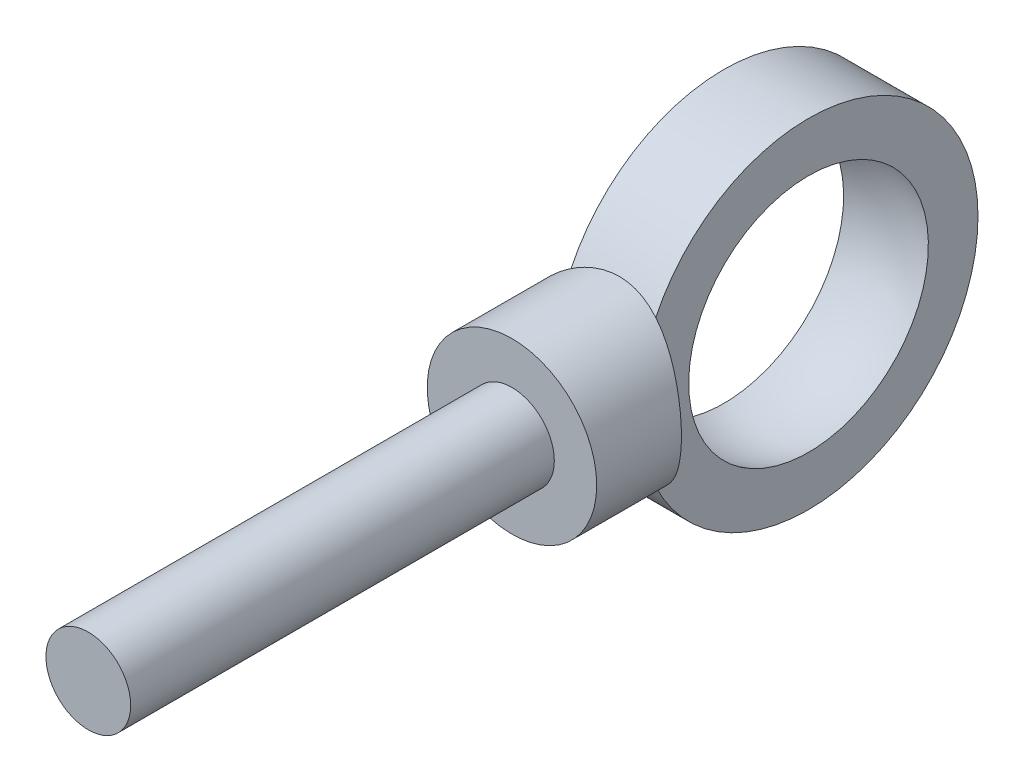
SolidWorks part; units mm, degrees
ref_plane "Front Plane" through (0, 0, 0) normal (0, 0, 1) x (1, 0, 0)
ref_plane "Top Plane" through (0, 0, 0) normal (0, 1, 0) x (1, 0, 0)
ref_plane "Right Plane" through (0, 0, 0) normal (1, 0, 0) x (0, 0, -1)
sketch "Sketch1" plane through (0, 0, 0) normal (0, 0, 1) x (1, 0, 0)
  line L0 (25.8616, 0) -> (0, 0) construction
  line L1 (0, 0) -> (0, 20) construction
  line L2 (-5, 20) -> (5, 20)
  line L3 (-5, 20) -> (-5, 0) construction
  line L4 (-5, 0) -> (5, 0) construction
  line L5 (5, 0) -> (5, 20) construction
  line L6 (-5, 20) -> (-5, 14.1421)
  line L7 (5, 20) -> (5, 14.1421)
  arc A0 (-5.0885, 14.1105) -> (-5, 14.1421) centre (0, 0) ccw construction
  arc A1 (-5, 14.1421) -> (5, 14.1421) centre (0, 0) cw
  point P7 (0, 20)
  dimension "D3" = 30
  dimension "D1" = 20
  dimension "D2" = 10
revolve "Revolve1" add sketch "Sketch1" angle 360 about L0
ref_plane "Plane1" through (0, 0, 30) normal (0, 0, 1) x (1, 0, 0)
sketch "Sketch2" plane through (0, 0, 30) normal (0, 0, 1) x (1, 0, 0)
  circle A0 centre (0, 0) radius 10
  dimension "D1" = 20
extrude "Boss-Extrude1" add sketch "Sketch2" against normal up to surface (10 mm away)
sketch "Sketch3" plane through (0, 0, 30) normal (0, 0, 1) x (1, 0, 0)
  circle A0 centre (0, 0) radius 5
  dimension "D1" = 10
extrude "Boss-Extrude2" add sketch "Sketch3" along normal blind 50
